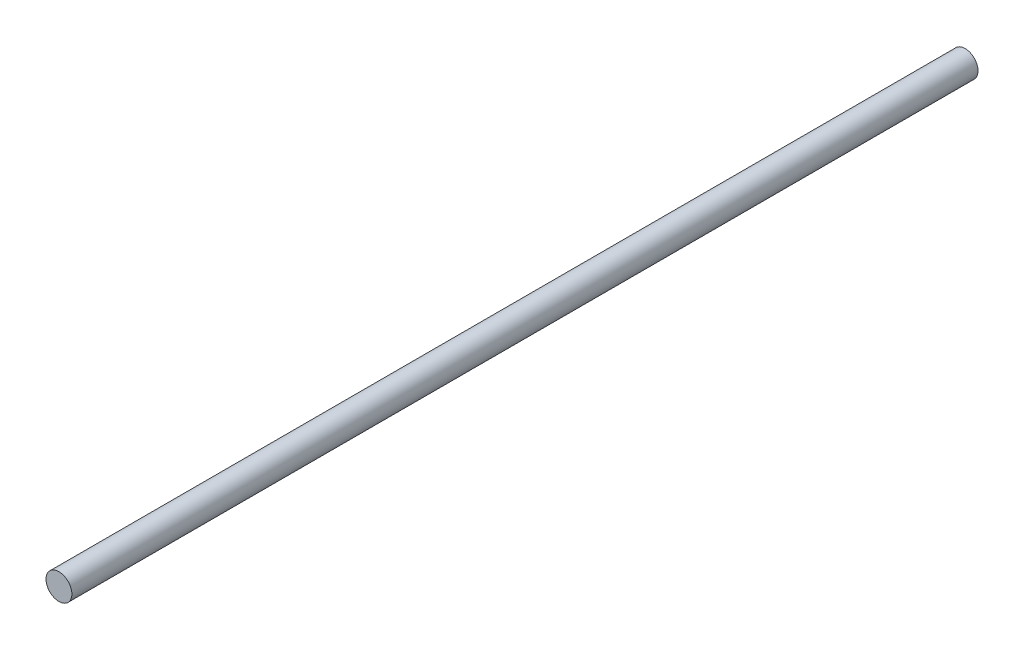
SolidWorks part; units mm, degrees
ref_plane "Front Plane" through (0, 0, 0) normal (0, 0, 1) x (1, 0, 0)
ref_plane "Top Plane" through (0, 0, 0) normal (0, 1, 0) x (1, 0, 0)
ref_plane "Right Plane" through (0, 0, 0) normal (1, 0, 0) x (0, 0, -1)
sketch "Sketch1" plane through (0, 0, 0) normal (0, 0, 1) x (1, 0, 0)
  circle A0 centre (0, 0) radius 4
  dimension "D1" = 8
extrude "Boss-Extrude1" add sketch "Sketch1" along normal blind 287.5
sketch "Sketch2" plane through (0, 0, 287.5) normal (0, 0, 1) x (1, 0, 0)
  circle A1 centre (0, 0) radius 4
  circle A2 centre (0, 0) radius 4
  dimension "D1" = 0
extrude "Boss-Extrude2" add sketch "Sketch2" along normal blind 45
sketch "Sketch3" plane through (0, 0, 0) normal (0, 0, -1) x (-1, 0, 0)
  circle A1 centre (0, 0) radius 4
  circle A2 centre (0, 0) radius 4
  dimension "D1" = 0
extrude "Cut-Extrude1" cut sketch "Sketch3" against normal blind 65
sketch "Sketch4" plane through (0, 0, 65) normal (0, 0, -1) x (-1, 0, 0)
  circle A1 centre (0, 0) radius 4
  circle A2 centre (0, 0) radius 4
  dimension "D1" = 0
move or copy body "Body-Move/Copy1" [suppressed] bodies to move or copy 101
extrude "Boss-Extrude5" add sketch "Sketch4" along normal blind 13
